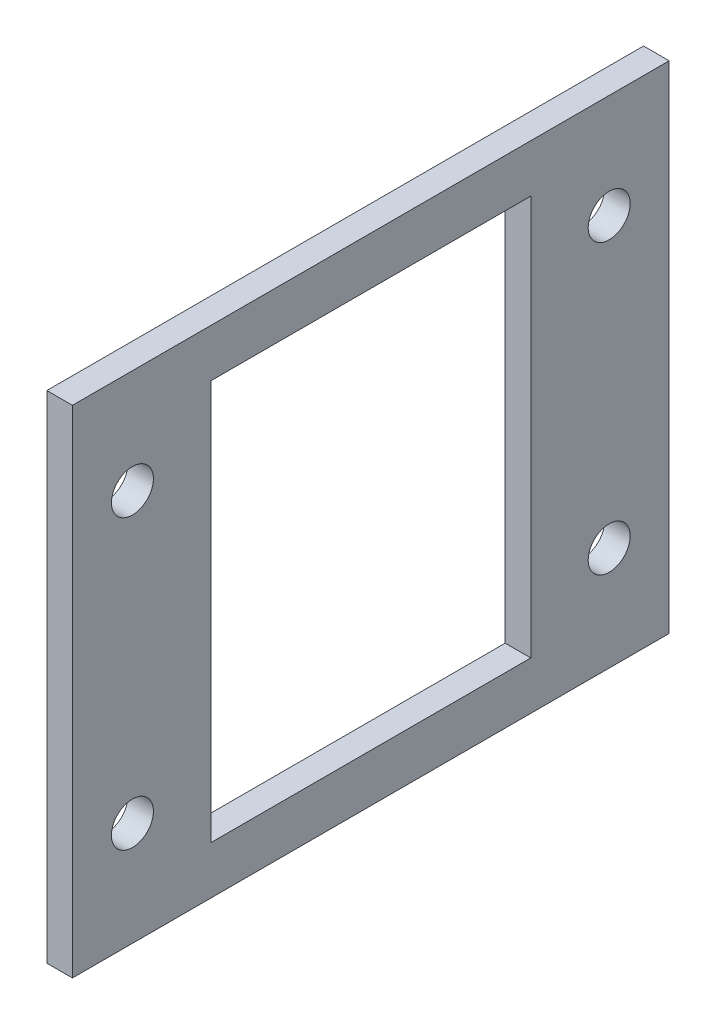
SolidWorks part; units mm, degrees
material "AISI 304"
ref_plane "Front Plane" through (0, 0, 0) normal (0, 0, 1) x (1, 0, 0)
ref_plane "Top Plane" through (0, 0, 0) normal (0, 1, 0) x (1, 0, 0)
ref_plane "Right Plane" through (0, 0, 0) normal (1, 0, 0) x (0, 0, -1)
sketch "Sketch1" plane through (0, 0, 0) normal (1, 0, 0) x (0, 0, -1)
  line L1 (0, 0) -> (74.6, 0)
  line L2 (0, 0) -> (0, 62)
  line L3 (0, 62) -> (74.6, 62)
  line L4 (74.6, 0) -> (74.6, 62)
  dimension "D1" = 74.6
  dimension "D2" = 62
extrude "Boss-Extrude1" add sketch "Sketch1" along normal blind 3.2
sketch "Sketch2" plane through (3.2, 0, 0) normal (1, 0, 0) x (0, 0, -1)
  line L0 (37.3, 62) -> (37.3, 0) construction
  line L1 (74.6, 62) -> (0, 62) construction
  line L2 (0, 0) -> (74.6, 0) construction
  line L3 (17.3, 56) -> (57.3, 6) construction
  line L4 (17.3, 6) -> (57.3, 6)
  line L5 (17.3, 6) -> (17.3, 56)
  line L6 (17.3, 56) -> (57.3, 56)
  line L7 (57.3, 6) -> (57.3, 56)
  point P6 (37.3, 56)
  point P8 (37.3, 31)
  point P12 (37.3, 31)
  point P13 (37.3, 0)
  dimension "D1" = 40
  dimension "D2" = 50
extrude "Cut-Extrude1" cut sketch "Sketch2" against normal up to next
sketch "Sketch3" plane through (0, 0, 0) normal (-1, 0, 0) x (0, 0, 1)
  circle A0 centre (-67.1, 13) radius 2.625
  circle A1 centre (-67.1, 49) radius 2.625
  circle A2 centre (-7.5, 49) radius 2.625
  circle A3 centre (-7.5, 13) radius 2.625
extrude "Cut-Extrude2" cut sketch "Sketch3" against normal up to next
